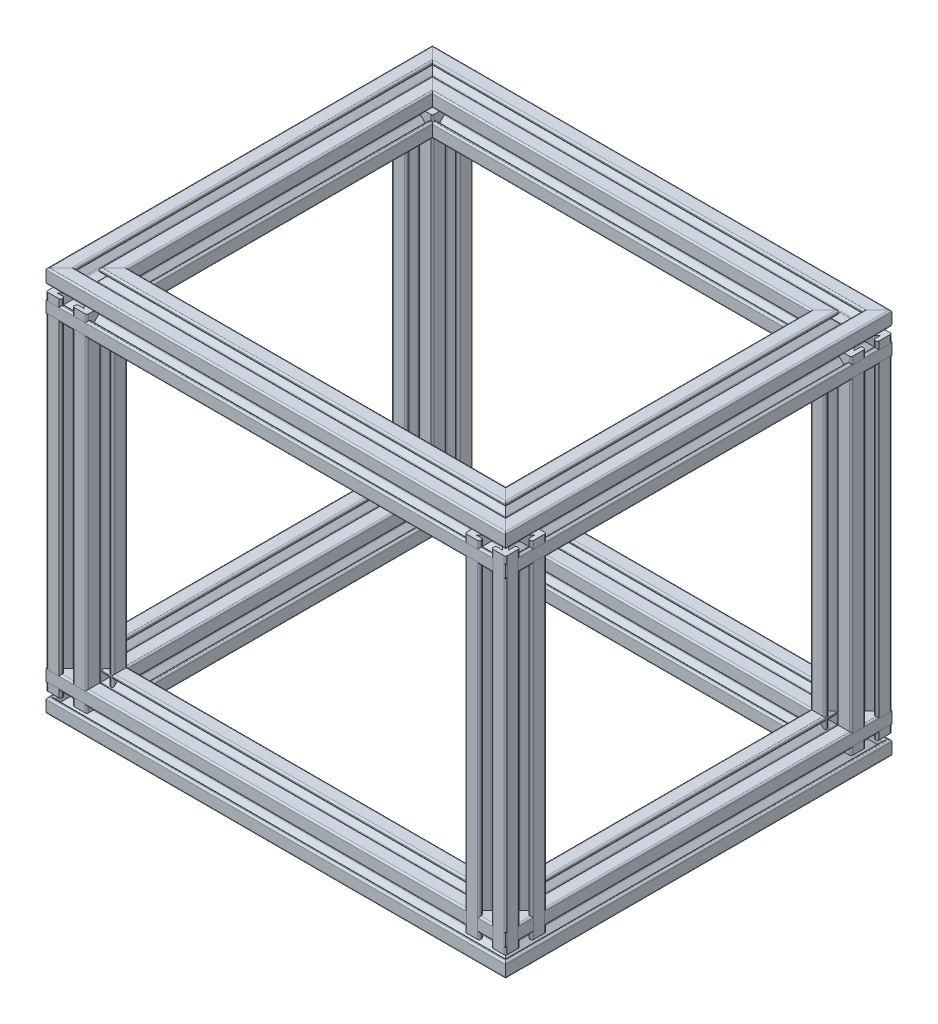
SolidWorks part; units mm, degrees
material "1060 Alloy"
material "1060 Alloy"
material "1060 Alloy"
material "1060 Alloy"
ref_plane "Front Plane" through (0, 0, 0) normal (0, 0, 1) x (1, 0, 0)
ref_plane "Top Plane" through (0, 0, 0) normal (0, 1, 0) x (1, 0, 0)
ref_plane "Right Plane" through (0, 0, 0) normal (1, 0, 0) x (0, 0, -1)
sketch "Sketch2" plane through (0, 0, 0) normal (0, 1, 0) x (1, 0, 0)
  line L1 (0, 0) -> (206, 0)
  line L2 (0, 0) -> (0, -170)
  line L3 (0, -170) -> (206, -170)
  line L4 (206, 0) -> (206, -170)
  dimension "D1" = 206
  dimension "D2" = 170
sketch "Sketch3" plane through (0, 0, 0) normal (0, 0, 1) x (1, 0, 0)
  line L0 (0, 0) -> (0, 170)
  line L1 (0, 170) -> (206, 170)
  line L2 (206, 170) -> (206, 0)
  dimension "D1" = 206
  dimension "D2" = 170
sketch "Sketch5" plane through (0, 0, 0) normal (1, 0, 0) x (0, 0, -1)
  line L0 (-170, 0) -> (-170, 170)
  line L1 (-170, 170) -> (0, 170)
  line L2 (0, 0) -> (0, 170) construction
  dimension "D1" = 170
ref_plane "Plane1" through (206, 0, 0) normal (1, 0, 0) x (0, 0, -1)
sketch "Sketch6" plane through (206, 0, 0) normal (1, 0, 0) x (0, 0, -1)
  line L0 (-170, 0) -> (-170, 170)
  line L1 (-170, 170) -> (0, 170)
  line L2 (0, 170) -> (0, 0) construction
  dimension "D1" = 170
  dimension "D2" = 170
ref_plane "Plane2" through (0, 0, 170) normal (0, 0, -1) x (-1, 0, 0)
sketch "Sketch7" plane through (0, 0, 170) normal (0, 0, -1) x (-1, 0, 0)
  line L0 (0, 170) -> (-206, 170)
other "Profile 4X4(1)"
ref_plane "Plane3" through (0, 0, 170) normal (0, 1, 0) x (0, 0, 1)
sketch "Sketch1" plane through (0, 0, 170) normal (0, 1, 0) x (0, 0, 1)
  line L0 (-3, 9.2) -> (-3, 8.8)
  line L1 (-2.2544, 4) -> (2.2544, 4)
  line L2 (-4, 2.2544) -> (-4, -2.2544)
  line L3 (-2.2544, -4) -> (2.2544, -4)
  line L4 (4, 2.2544) -> (4, -2.2544)
  line L7 (-6.5858, 8) -> (-3.8, 8)
  line L8 (-8, 6.5858) -> (-8, 3.8)
  line L9 (-6.5858, -8) -> (-3.8, -8)
  line L10 (8, 6.5858) -> (8, 3.8)
  line L12 (9.7657, -9.7657) -> (10, -10) construction
  line L13 (-9.2, 10) -> (-3.8, 10)
  line L14 (-10, 9.2) -> (-10, 3.8)
  line L15 (-9.2, -10) -> (-3.8, -10)
  line L16 (10, 9.2) -> (10, 3.8)
  line L17 (-10, 10) -> (-9.7657, 9.7657) construction
  line L18 (-10, -10) -> (-9.7657, -9.7657) construction
  line L21 (3, 9.2) -> (3, 8.8)
  line L22 (3, -9.2) -> (3, -8.8)
  line L23 (-3, -9.2) -> (-3, -8.8)
  line L24 (3.8, 10) -> (9.2, 10)
  line L25 (3.8, 8) -> (6.5858, 8)
  line L26 (-9.2, 3) -> (-8.8, 3)
  line L27 (9.2, 3) -> (8.8, 3)
  line L28 (9.2, -3) -> (8.8, -3)
  line L29 (-9.2, -3) -> (-8.8, -3)
  line L30 (-10, -3.8) -> (-10, -9.2)
  line L31 (-8, -3.8) -> (-8, -6.5858)
  line L32 (8, -3.8) -> (8, -6.5858)
  line L33 (10, -3.8) -> (10, -9.2)
  line L34 (3.8, -8) -> (6.5858, -8)
  line L35 (3.8, -10) -> (9.2, -10)
  line L36 (6.5858, 8) -> (2.8201, 4.2343)
  line L37 (8, 6.5858) -> (4.2343, 2.8201)
  line L38 (8, -6.5858) -> (4.2343, -2.8201)
  line L39 (6.5858, -8) -> (2.8201, -4.2343)
  line L40 (-6.5858, -8) -> (-2.8201, -4.2343)
  line L41 (-8, -6.5858) -> (-4.2343, -2.8201)
  line L42 (-8, 6.5858) -> (-4.2343, 2.8201)
  line L43 (-6.5858, 8) -> (-2.8201, 4.2343)
  line L47 (9.7657, 9.7657) -> (10, 10) construction
  circle A0 centre (0, 0) radius 2
  arc A1 (9.2, -3) -> (10, -3.8) centre (9.2, -3.8) cw
  arc A2 (8.8, -3) -> (8, -3.8) centre (8.8, -3.8) ccw
  arc A3 (3, -9.2) -> (3.8, -10) centre (3.8, -9.2) ccw
  arc A4 (3, -8.8) -> (3.8, -8) centre (3.8, -8.8) cw
  arc A5 (-3, -9.2) -> (-3.8, -10) centre (-3.8, -9.2) cw
  arc A6 (-3, -8.8) -> (-3.8, -8) centre (-3.8, -8.8) ccw
  arc A7 (-8.8, -3) -> (-8, -3.8) centre (-8.8, -3.8) cw
  arc A8 (-9.2, -3) -> (-10, -3.8) centre (-9.2, -3.8) ccw
  arc A9 (-10, -9.2) -> (-9.2, -10) centre (-9.2, -9.2) ccw
  arc A10 (9.2, -10) -> (10, -9.2) centre (9.2, -9.2) ccw
  arc A11 (9.2, 10) -> (10, 9.2) centre (9.2, 9.2) cw
  arc A12 (-9.2, 10) -> (-10, 9.2) centre (-9.2, 9.2) ccw
  arc A13 (9.2, 3) -> (10, 3.8) centre (9.2, 3.8) ccw
  arc A14 (8.8, 3) -> (8, 3.8) centre (8.8, 3.8) cw
  arc A15 (3, 9.2) -> (3.8, 10) centre (3.8, 9.2) cw
  arc A16 (3, 8.8) -> (3.8, 8) centre (3.8, 8.8) ccw
  arc A17 (-3, 9.2) -> (-3.8, 10) centre (-3.8, 9.2) ccw
  arc A18 (-3, 8.8) -> (-3.8, 8) centre (-3.8, 8.8) cw
  arc A19 (-8.8, 3) -> (-8, 3.8) centre (-8.8, 3.8) ccw
  arc A20 (-9.2, 3) -> (-10, 3.8) centre (-9.2, 3.8) cw
  arc A21 (-2.8201, 4.2343) -> (-2.2544, 4) centre (-2.2544, 4.8) ccw
  arc A22 (4.2343, 2.8201) -> (4, 2.2544) centre (4.8, 2.2544) ccw
  arc A23 (2.8201, 4.2343) -> (2.2544, 4) centre (2.2544, 4.8) cw
  arc A24 (4.2343, -2.8201) -> (4, -2.2544) centre (4.8, -2.2544) cw
  arc A25 (2.8201, -4.2343) -> (2.2544, -4) centre (2.2544, -4.8) ccw
  arc A26 (-2.8201, -4.2343) -> (-2.2544, -4) centre (-2.2544, -4.8) cw
  arc A27 (-4.2343, -2.8201) -> (-4, -2.2544) centre (-4.8, -2.2544) ccw
  arc A28 (-4.2343, 2.8201) -> (-4, 2.2544) centre (-4.8, 2.2544) cw
  point P7 (0, 0)
  point P10 (-2.5858, 4)
  point P53 (10, -3)
  point P56 (8, -3)
  point P59 (3, -10)
  point P62 (3, -8)
  point P65 (-3, -10)
  point P68 (-3, -8)
  point P71 (-8, -3)
  point P74 (-10, -3)
  point P89 (10, 3)
  point P92 (8, 3)
  point P95 (3, 10)
  point P98 (3, 8)
  point P101 (-3, 10)
  point P104 (-3, 8)
  point P107 (-8, 3)
  point P110 (-10, 3)
  point P116 (4, 2.5858)
  point P119 (2.5858, 4)
  point P122 (4, -2.5858)
  point P125 (2.5858, -4)
  point P128 (-2.5858, -4)
  point P131 (-4, -2.5858)
  point P134 (-4, 2.5858)
  dimension "D3" = 4
  dimension "D11" = 0.8
  dimension "D12" = 0.8
  dimension "D2" = 0.8
  dimension "D4" = 20
  dimension "D6" = 20
  dimension "D8" = 7
  dimension "D9" = 7
other "Profile 4X4(2)"
ref_plane "Plane4" through (0, 170, 170) normal (0, 0, -1) x (0, 1, 0)
sketch "Sketch11" plane through (0, 170, 170) normal (0, 0, -1) x (0, 1, 0)
  line L0 (-3, 9.2) -> (-3, 8.8)
  line L1 (-2.2544, 4) -> (2.2544, 4)
  line L2 (-4, 2.2544) -> (-4, -2.2544)
  line L3 (-2.2544, -4) -> (2.2544, -4)
  line L4 (4, 2.2544) -> (4, -2.2544)
  line L7 (-6.5858, 8) -> (-3.8, 8)
  line L8 (-8, 6.5858) -> (-8, 3.8)
  line L9 (-6.5858, -8) -> (-3.8, -8)
  line L10 (8, 6.5858) -> (8, 3.8)
  line L12 (9.7657, -9.7657) -> (10, -10) construction
  line L13 (-9.2, 10) -> (-3.8, 10)
  line L14 (-10, 9.2) -> (-10, 3.8)
  line L15 (-9.2, -10) -> (-3.8, -10)
  line L16 (10, 9.2) -> (10, 3.8)
  line L17 (-10, 10) -> (-9.7657, 9.7657) construction
  line L18 (-10, -10) -> (-9.7657, -9.7657) construction
  line L21 (3, 9.2) -> (3, 8.8)
  line L22 (3, -9.2) -> (3, -8.8)
  line L23 (-3, -9.2) -> (-3, -8.8)
  line L24 (3.8, 10) -> (9.2, 10)
  line L25 (3.8, 8) -> (6.5858, 8)
  line L26 (-9.2, 3) -> (-8.8, 3)
  line L27 (9.2, 3) -> (8.8, 3)
  line L28 (9.2, -3) -> (8.8, -3)
  line L29 (-9.2, -3) -> (-8.8, -3)
  line L30 (-10, -3.8) -> (-10, -9.2)
  line L31 (-8, -3.8) -> (-8, -6.5858)
  line L32 (8, -3.8) -> (8, -6.5858)
  line L33 (10, -3.8) -> (10, -9.2)
  line L34 (3.8, -8) -> (6.5858, -8)
  line L35 (3.8, -10) -> (9.2, -10)
  line L36 (6.5858, 8) -> (2.8201, 4.2343)
  line L37 (8, 6.5858) -> (4.2343, 2.8201)
  line L38 (8, -6.5858) -> (4.2343, -2.8201)
  line L39 (6.5858, -8) -> (2.8201, -4.2343)
  line L40 (-6.5858, -8) -> (-2.8201, -4.2343)
  line L41 (-8, -6.5858) -> (-4.2343, -2.8201)
  line L42 (-8, 6.5858) -> (-4.2343, 2.8201)
  line L43 (-6.5858, 8) -> (-2.8201, 4.2343)
  line L47 (9.7657, 9.7657) -> (10, 10) construction
  circle A0 centre (0, 0) radius 2
  arc A1 (9.2, -3) -> (10, -3.8) centre (9.2, -3.8) cw
  arc A2 (8.8, -3) -> (8, -3.8) centre (8.8, -3.8) ccw
  arc A3 (3, -9.2) -> (3.8, -10) centre (3.8, -9.2) ccw
  arc A4 (3, -8.8) -> (3.8, -8) centre (3.8, -8.8) cw
  arc A5 (-3, -9.2) -> (-3.8, -10) centre (-3.8, -9.2) cw
  arc A6 (-3, -8.8) -> (-3.8, -8) centre (-3.8, -8.8) ccw
  arc A7 (-8.8, -3) -> (-8, -3.8) centre (-8.8, -3.8) cw
  arc A8 (-9.2, -3) -> (-10, -3.8) centre (-9.2, -3.8) ccw
  arc A9 (-10, -9.2) -> (-9.2, -10) centre (-9.2, -9.2) ccw
  arc A10 (9.2, -10) -> (10, -9.2) centre (9.2, -9.2) ccw
  arc A11 (9.2, 10) -> (10, 9.2) centre (9.2, 9.2) cw
  arc A12 (-9.2, 10) -> (-10, 9.2) centre (-9.2, 9.2) ccw
  arc A13 (9.2, 3) -> (10, 3.8) centre (9.2, 3.8) ccw
  arc A14 (8.8, 3) -> (8, 3.8) centre (8.8, 3.8) cw
  arc A15 (3, 9.2) -> (3.8, 10) centre (3.8, 9.2) cw
  arc A16 (3, 8.8) -> (3.8, 8) centre (3.8, 8.8) ccw
  arc A17 (-3, 9.2) -> (-3.8, 10) centre (-3.8, 9.2) ccw
  arc A18 (-3, 8.8) -> (-3.8, 8) centre (-3.8, 8.8) cw
  arc A19 (-8.8, 3) -> (-8, 3.8) centre (-8.8, 3.8) ccw
  arc A20 (-9.2, 3) -> (-10, 3.8) centre (-9.2, 3.8) cw
  arc A21 (-2.8201, 4.2343) -> (-2.2544, 4) centre (-2.2544, 4.8) ccw
  arc A22 (4.2343, 2.8201) -> (4, 2.2544) centre (4.8, 2.2544) ccw
  arc A23 (2.8201, 4.2343) -> (2.2544, 4) centre (2.2544, 4.8) cw
  arc A24 (4.2343, -2.8201) -> (4, -2.2544) centre (4.8, -2.2544) cw
  arc A25 (2.8201, -4.2343) -> (2.2544, -4) centre (2.2544, -4.8) ccw
  arc A26 (-2.8201, -4.2343) -> (-2.2544, -4) centre (-2.2544, -4.8) cw
  arc A27 (-4.2343, -2.8201) -> (-4, -2.2544) centre (-4.8, -2.2544) ccw
  arc A28 (-4.2343, 2.8201) -> (-4, 2.2544) centre (-4.8, 2.2544) cw
  point P7 (0, 0)
  point P10 (-2.5858, 4)
  point P53 (10, -3)
  point P56 (8, -3)
  point P59 (3, -10)
  point P62 (3, -8)
  point P65 (-3, -10)
  point P68 (-3, -8)
  point P71 (-8, -3)
  point P74 (-10, -3)
  point P89 (10, 3)
  point P92 (8, 3)
  point P95 (3, 10)
  point P98 (3, 8)
  point P101 (-3, 10)
  point P104 (-3, 8)
  point P107 (-8, 3)
  point P110 (-10, 3)
  point P116 (4, 2.5858)
  point P119 (2.5858, 4)
  point P122 (4, -2.5858)
  point P125 (2.5858, -4)
  point P128 (-2.5858, -4)
  point P131 (-4, -2.5858)
  point P134 (-4, 2.5858)
  dimension "D3" = 4
  dimension "D11" = 0.8
  dimension "D12" = 0.8
  dimension "D2" = 0.8
  dimension "D4" = 20
  dimension "D6" = 20
  dimension "D8" = 7
  dimension "D9" = 7
other "Profile 4X4(3)"
ref_plane "Plane5" through (0, 170, 170) normal (1, 0, 0) x (0, -1, 0)
sketch "Sketch12" plane through (0, 170, 170) normal (1, 0, 0) x (0, -1, 0)
  line L0 (-3, 9.2) -> (-3, 8.8)
  line L1 (-2.2544, 4) -> (2.2544, 4)
  line L2 (-4, 2.2544) -> (-4, -2.2544)
  line L3 (-2.2544, -4) -> (2.2544, -4)
  line L4 (4, 2.2544) -> (4, -2.2544)
  line L7 (-6.5858, 8) -> (-3.8, 8)
  line L8 (-8, 6.5858) -> (-8, 3.8)
  line L9 (-6.5858, -8) -> (-3.8, -8)
  line L10 (8, 6.5858) -> (8, 3.8)
  line L12 (9.7657, -9.7657) -> (10, -10) construction
  line L13 (-9.2, 10) -> (-3.8, 10)
  line L14 (-10, 9.2) -> (-10, 3.8)
  line L15 (-9.2, -10) -> (-3.8, -10)
  line L16 (10, 9.2) -> (10, 3.8)
  line L17 (-10, 10) -> (-9.7657, 9.7657) construction
  line L18 (-10, -10) -> (-9.7657, -9.7657) construction
  line L21 (3, 9.2) -> (3, 8.8)
  line L22 (3, -9.2) -> (3, -8.8)
  line L23 (-3, -9.2) -> (-3, -8.8)
  line L24 (3.8, 10) -> (9.2, 10)
  line L25 (3.8, 8) -> (6.5858, 8)
  line L26 (-9.2, 3) -> (-8.8, 3)
  line L27 (9.2, 3) -> (8.8, 3)
  line L28 (9.2, -3) -> (8.8, -3)
  line L29 (-9.2, -3) -> (-8.8, -3)
  line L30 (-10, -3.8) -> (-10, -9.2)
  line L31 (-8, -3.8) -> (-8, -6.5858)
  line L32 (8, -3.8) -> (8, -6.5858)
  line L33 (10, -3.8) -> (10, -9.2)
  line L34 (3.8, -8) -> (6.5858, -8)
  line L35 (3.8, -10) -> (9.2, -10)
  line L36 (6.5858, 8) -> (2.8201, 4.2343)
  line L37 (8, 6.5858) -> (4.2343, 2.8201)
  line L38 (8, -6.5858) -> (4.2343, -2.8201)
  line L39 (6.5858, -8) -> (2.8201, -4.2343)
  line L40 (-6.5858, -8) -> (-2.8201, -4.2343)
  line L41 (-8, -6.5858) -> (-4.2343, -2.8201)
  line L42 (-8, 6.5858) -> (-4.2343, 2.8201)
  line L43 (-6.5858, 8) -> (-2.8201, 4.2343)
  line L47 (9.7657, 9.7657) -> (10, 10) construction
  circle A0 centre (0, 0) radius 2
  arc A1 (9.2, -3) -> (10, -3.8) centre (9.2, -3.8) cw
  arc A2 (8.8, -3) -> (8, -3.8) centre (8.8, -3.8) ccw
  arc A3 (3, -9.2) -> (3.8, -10) centre (3.8, -9.2) ccw
  arc A4 (3, -8.8) -> (3.8, -8) centre (3.8, -8.8) cw
  arc A5 (-3, -9.2) -> (-3.8, -10) centre (-3.8, -9.2) cw
  arc A6 (-3, -8.8) -> (-3.8, -8) centre (-3.8, -8.8) ccw
  arc A7 (-8.8, -3) -> (-8, -3.8) centre (-8.8, -3.8) cw
  arc A8 (-9.2, -3) -> (-10, -3.8) centre (-9.2, -3.8) ccw
  arc A9 (-10, -9.2) -> (-9.2, -10) centre (-9.2, -9.2) ccw
  arc A10 (9.2, -10) -> (10, -9.2) centre (9.2, -9.2) ccw
  arc A11 (9.2, 10) -> (10, 9.2) centre (9.2, 9.2) cw
  arc A12 (-9.2, 10) -> (-10, 9.2) centre (-9.2, 9.2) ccw
  arc A13 (9.2, 3) -> (10, 3.8) centre (9.2, 3.8) ccw
  arc A14 (8.8, 3) -> (8, 3.8) centre (8.8, 3.8) cw
  arc A15 (3, 9.2) -> (3.8, 10) centre (3.8, 9.2) cw
  arc A16 (3, 8.8) -> (3.8, 8) centre (3.8, 8.8) ccw
  arc A17 (-3, 9.2) -> (-3.8, 10) centre (-3.8, 9.2) ccw
  arc A18 (-3, 8.8) -> (-3.8, 8) centre (-3.8, 8.8) cw
  arc A19 (-8.8, 3) -> (-8, 3.8) centre (-8.8, 3.8) ccw
  arc A20 (-9.2, 3) -> (-10, 3.8) centre (-9.2, 3.8) cw
  arc A21 (-2.8201, 4.2343) -> (-2.2544, 4) centre (-2.2544, 4.8) ccw
  arc A22 (4.2343, 2.8201) -> (4, 2.2544) centre (4.8, 2.2544) ccw
  arc A23 (2.8201, 4.2343) -> (2.2544, 4) centre (2.2544, 4.8) cw
  arc A24 (4.2343, -2.8201) -> (4, -2.2544) centre (4.8, -2.2544) cw
  arc A25 (2.8201, -4.2343) -> (2.2544, -4) centre (2.2544, -4.8) ccw
  arc A26 (-2.8201, -4.2343) -> (-2.2544, -4) centre (-2.2544, -4.8) cw
  arc A27 (-4.2343, -2.8201) -> (-4, -2.2544) centre (-4.8, -2.2544) ccw
  arc A28 (-4.2343, 2.8201) -> (-4, 2.2544) centre (-4.8, 2.2544) cw
  point P7 (0, 0)
  point P10 (-2.5858, 4)
  point P53 (10, -3)
  point P56 (8, -3)
  point P59 (3, -10)
  point P62 (3, -8)
  point P65 (-3, -10)
  point P68 (-3, -8)
  point P71 (-8, -3)
  point P74 (-10, -3)
  point P89 (10, 3)
  point P92 (8, 3)
  point P95 (3, 10)
  point P98 (3, 8)
  point P101 (-3, 10)
  point P104 (-3, 8)
  point P107 (-8, 3)
  point P110 (-10, 3)
  point P116 (4, 2.5858)
  point P119 (2.5858, 4)
  point P122 (4, -2.5858)
  point P125 (2.5858, -4)
  point P128 (-2.5858, -4)
  point P131 (-4, -2.5858)
  point P134 (-4, 2.5858)
  dimension "D3" = 4
  dimension "D11" = 0.8
  dimension "D12" = 0.8
  dimension "D2" = 0.8
  dimension "D4" = 20
  dimension "D6" = 20
  dimension "D8" = 7
  dimension "D9" = 7
other "Trim/Extend1"
other "Trim/Extend2"
other "Trim/Extend3"
other "Trim/Extend4"
other "Trim/Extend5"
other "Trim/Extend6"
other "Trim/Extend7"
other "Trim/Extend8"
